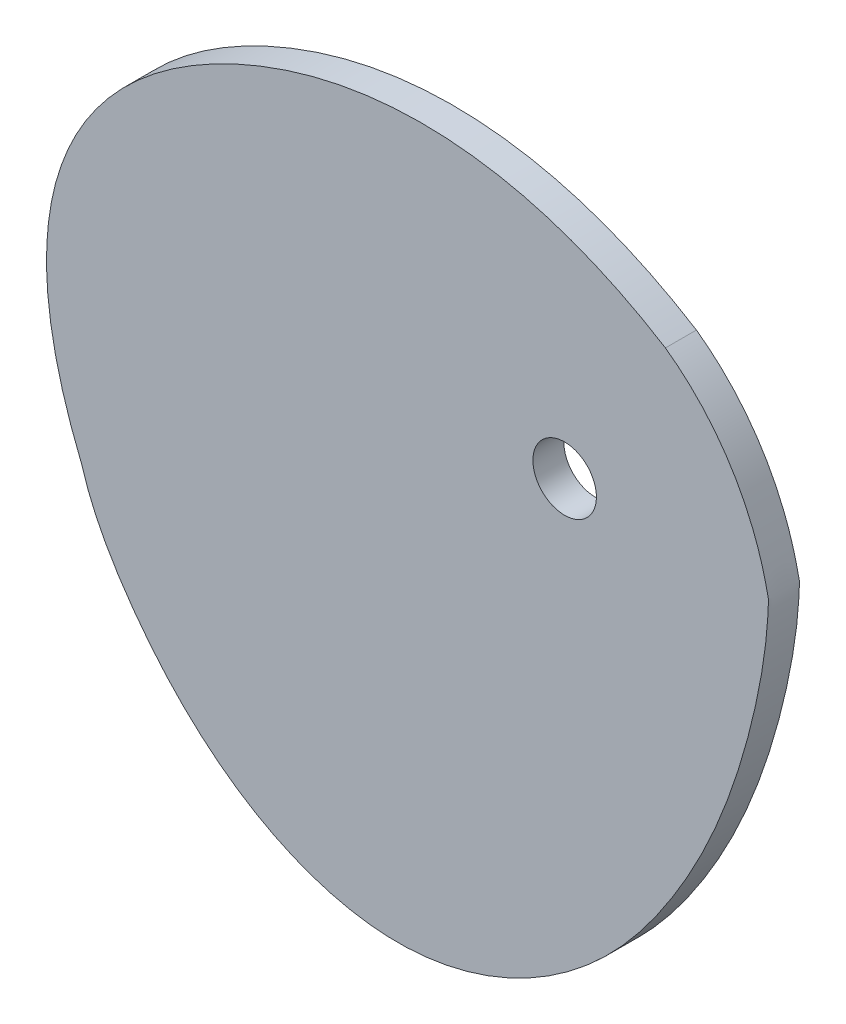
SolidWorks part; units mm, degrees
ref_plane "Front Plane" through (0, 0, 0) normal (0, 0, 1) x (1, 0, 0)
ref_plane "Top Plane" through (0, 0, 0) normal (0, 1, 0) x (1, 0, 0)
ref_plane "Right Plane" through (0, 0, 0) normal (1, 0, 0) x (0, 0, -1)
curve "Curve1"
sketch "Sketch1" plane through (0, 0, 0) normal (0, 0, 1) x (1, 0, 0)
  circle A0 centre (0, 0) radius 3.075
  spline S0 degree 3 poles (-46.72, -22.2048) (-56.2585, 0.9012) (-32.2758, 25.8799) (-3.4263, 24.0431) (9.7507, 15.83) knots 0 0 0 0 0.5031 0.999856 0.999856 0.999856 0.999856
  spline S1 degree 3 number of poles 140 (-46.72, -22.2048) -> (9.7507, 15.83)
  point P0 (0, 0)
  point P6 (-45.3798, -25.7851)
  point P8 (-46.72, -22.2048)
  dimension "D1" = 6.15
extrude "Boss-Extrude1" add sketch "Sketch1" along normal mid plane 3
sketch "Sketch4" [suppressed] plane through (0, 0, 1.5) normal (0, 0, 1) x (1, 0, 0)
  line L0 (17.5773, -21.2942) -> (-0.4059, -51.7692) construction
  line L1 (-48.8051, -15.5697) -> (-20.0826, 24.9009) construction
  circle A0 centre (-13.2083, -15.9321) radius 29.2387 construction
  spline S0 degree 3 number of poles 363 (20.4693, 0) -> (20.4693, 0) construction
  point P5 (-13.488, -5.936)
  point P6 (-3.3675, -25.0764)
  point P11 (-25.0038, -24.2708)
  point P12 (-13.9531, -18.4277)
  dimension "D1" = 3
  dimension "D2" = 10
hole_wizard "M4 Clearance Hole1" [suppressed] positions "Sketch5" profile "Sketch7" hole size "M4" standard "ANSI Metric"
sketch "Sketch5" [suppressed] plane through (0, 0, 1.5) normal (0, 0, 1) x (1, 0, 0)
  point P0 (-13.488, -5.936)
  point P3 (-3.3675, -25.0764)
  point P6 (-25.0038, -24.2708)
sketch "Sketch7" plane through (-13.488, -5.936, 1.5) normal (1, 0, 0) x (0, -1, 0)
  line L0 (0, 0) -> (0, 3)
  line L1 (0, 3) -> (2.15, 3)
  line L2 (2.15, 3) -> (2.15, 0)
  line L5 (2.15, 0) -> (0, 0)
  line L11 (0, -6.35) -> (0, 107.95) construction
  dimension "Thru Hole Dia." = 4.3
  dimension "Thru Hole Depth" = 3
sketch "Sketch8" [suppressed] plane through (0, 0, 1.5) normal (0, 0, 1) x (1, 0, 0)
  line L5 (-11.09, -40.8947) -> (-20.9198, -47.7776) construction
  line L8 (-28.4462, -45.3019) -> (-27.0696, -47.2679)
  line L9 (-15.2394, -42.4024) -> (-16.8454, -40.1088)
  line L10 (-16.8454, -40.1088) -> (-27.0696, -47.2679)
  line L11 (-6.9178, -29.0068) -> (-3.3617, -34.0855) construction
  line L13 (-6.9178, -29.0068) -> (-18.7955, -37.3237)
  line L15 (-15.2394, -42.4024) -> (-3.3617, -34.0855)
  line L16 (-18.7955, -37.3237) -> (-18.222, -38.1428)
  line L17 (-18.222, -38.1428) -> (-28.4462, -45.3019)
  line L18 (-6.9178, -29.0068) -> (-6.5083, -28.72)
  line L19 (-6.5083, -28.72) -> (-2.9521, -33.7988)
  line L22 (-3.3617, -34.0855) -> (-2.9521, -33.7988)
  spline S1 degree 3 number of poles 363 (20.4693, 0) -> (20.4693, 0) construction
  dimension "D6" = 2.4
  dimension "D1" = 14.5
  dimension "D2" = 2.8
  dimension "D3" = 12
  dimension "D4" = 0.5
  dimension "D8" = 27
  dimension "D9" = 14.5
  dimension "D10" = 6.2
  dimension "D11" = 1
extrude "Cut-Extrude1" [suppressed] cut sketch "Sketch8" against normal through all both and the other way through all
fillet "Fillet1" [suppressed] radius 10
sketch "Sketch10" [suppressed] plane through (0, 0, 0) normal (0, 0, 1) x (1, 0, 0)
  line L1 (-8.5177, -31.4464) -> (-10.3214, -44.6038) construction
  line L2 (-22.8408, -43.8925) -> (-20.9018, -29.7487) construction
  line L3 (-8.5177, -31.4464) -> (-10.3214, -44.6038)
  line L4 (-22.8408, -43.8925) -> (-20.9018, -29.7487)
  circle A6 centre (-13.0442, -46.0588) radius 1.5
  arc A7 (-10.3214, -44.6038) -> (-7.077, -47.3226) centre (-7.8445, -44.9433) ccw construction
  arc A8 (-8.5177, -31.4464) -> (-20.9018, -29.7487) centre (-14.7098, -30.5976) ccw construction
  arc A9 (-26.388, -45.8122) -> (-22.8408, -43.8925) centre (-25.3176, -43.5529) ccw construction
  arc A10 (-10.3214, -44.6038) -> (-7.077, -47.3226) centre (-7.8445, -44.9433) ccw
  arc A11 (-8.5177, -31.4464) -> (-20.9018, -29.7487) centre (-14.7098, -30.5976) ccw
  arc A12 (-26.388, -45.8122) -> (-22.8408, -43.8925) centre (-25.3176, -43.5529) ccw
  spline S1 degree 3 number of poles 363 (-7.077, -47.3226) -> (-26.388, -45.8122) construction
  spline S2 degree 3 number of poles 213 (-7.077, -47.3226) -> (-26.388, -45.8122)
  spline S4 degree 3 number of poles 165 (-53.4212, -32.1303) -> (-53.4212, -32.1303)
  spline S5 degree 3 number of poles 165 (-53.4212, -32.1303) -> (-53.4212, -32.1303)
  dimension "D2" = 3
  dimension "D3" = 2.5
  dimension "D1" = 10
extrude "Boss-Extrude5" [suppressed] add sketch "Sketch10" along normal mid plane 1.5
sketch "Sketch11" [suppressed] plane through (0, 0, 0) normal (0, 0, 1) x (1, 0, 0)
  point P0 (-7.234, 7.8407)
  point P1 (10.4072, 2.3444)
  point P3 (-3.1732, -10.1851)
hole_wizard "M2x0.4 Tapped Hole1" [suppressed] positions "Sketch12" profile "Sketch13" tap size "M2x0.4" standard "ANSI Metric"
sketch "Sketch12" [suppressed] plane through (0, 0, -1.5) normal (0, 0, -1) x (-1, 0, 0)
  point P0 (7.234, 7.8407)
  point P3 (-10.4072, 2.3444)
  point P6 (3.1732, -10.1851)
sketch "Sketch13" plane through (-7.234, 7.8407, -1.5) normal (1, 0, 0) x (0, 1, 0)
  line L0 (0, 0) -> (0, 3)
  line L1 (0, 3) -> (0.7, 3)
  line L2 (0.7, 3) -> (0.7, 0)
  line L5 (0.7, 0) -> (0, 0)
  line L11 (0, -6.35) -> (0, 107.95) construction
  dimension "Thru Tap Drill Dia." = 1.4
  dimension "Thru Tap Drill Depth" = 3
cosmetic thread "Hole Thread1" [suppressed] parameters "D2"=2
cosmetic thread "Hole Thread2" [suppressed] parameters "D2"=2
cosmetic thread "Hole Thread3" [suppressed] parameters "D2"=2
fillet "Fillet2" [suppressed] radius 1.5
sketch "Sketch14" plane through (0, 0, 1.5) normal (0, 0, 1) x (1, 0, 0)
  circle A0 centre (-12.5246, -41.0492) radius 1.05 construction
  circle A1 centre (0, -39.819) radius 1.05
  dimension "D1" = 2.1
  dimension "D2" = 2.1
extrude "Cut-Extrude2" [suppressed] cut sketch "Sketch14" against normal through all
sketch "Sketch15" [suppressed] plane through (0, 0, 0.75) normal (0, 0, 1) x (1, 0, 0)
  circle A0 centre (-24.2994, -39.0947) radius 1.1
  circle A1 centre (-14.3282, -44.0575) radius 1.1
extrude "Cut-Extrude3" [suppressed] cut sketch "Sketch15" against normal blind 10
sketch "Sketch16" [suppressed] plane through (0, 0, 0.75) normal (0, 0, 1) x (1, 0, 0)
  circle A0 centre (-5.523, -52.2474) radius 1.15
  circle A1 centre (5.4449, -44.5935) radius 1.15
  dimension "D1" = 2.3
  dimension "D2" = 2.3
extrude "Cut-Extrude4" [suppressed] cut sketch "Sketch16" against normal blind 10
fillet "Fillet3" [suppressed] radius 0.4
fillet "Fillet4" [suppressed] radius 1.25
